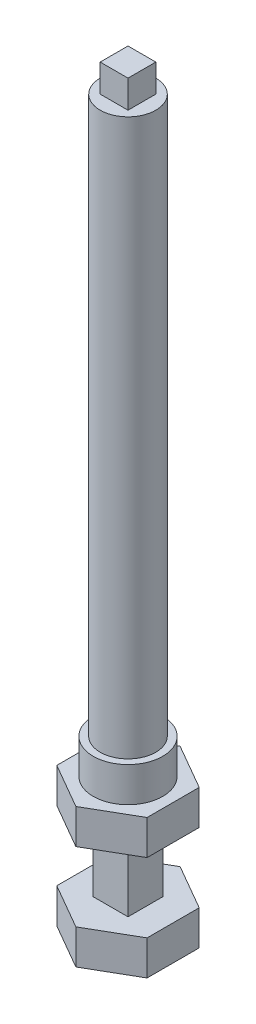
SolidWorks part; units mm, degrees
ref_plane "Front Plane" through (0, 0, 0) normal (0, 0, 1) x (1, 0, 0)
ref_plane "Top Plane" through (0, 0, 0) normal (0, 1, 0) x (1, 0, 0)
ref_plane "Right Plane" through (0, 0, 0) normal (1, 0, 0) x (0, 0, -1)
sketch "Sketch1" plane through (0, 0, 0) normal (0, 1, 0) x (1, 0, 0)
  line L1 (2.5, -2.5) -> (-2.5, -2.5)
  line L2 (2.5, -2.5) -> (2.5, 2.5)
  line L3 (2.5, 2.5) -> (-2.5, 2.5)
  line L4 (-2.5, -2.5) -> (-2.5, 2.5)
  line L5 (2.5, -2.5) -> (-2.5, 2.5) construction
  line L6 (2.5, 2.5) -> (-2.5, -2.5) construction
  point P0 (0, 0)
  dimension "D1" = 5
  dimension "D2" = 5
extrude "Boss-Extrude1" add sketch "Sketch1" along normal blind 10
sketch "Sketch2" plane through (0, 0, 0) normal (0, -1, 0) x (1, 0, 0)
  line L5 (0, 7.5) -> (-6.4952, 3.75)
  line L6 (-6.4952, 3.75) -> (-6.4952, -3.75)
  line L7 (-6.4952, -3.75) -> (0, -7.5)
  line L8 (0, -7.5) -> (6.4952, -3.75)
  line L9 (6.4952, -3.75) -> (6.4952, 3.75)
  line L10 (6.4952, 3.75) -> (0, 7.5)
  circle A0 centre (0, 0) radius 6.4952 construction
  point P0 (0, 0)
  dimension "D1" = 15
extrude "Boss-Extrude2" add sketch "Sketch2" along normal blind 5
sketch "Sketch3" plane through (0, 10, 0) normal (0, 1, 0) x (1, 0, 0)
  line L6 (0, -7.5) -> (6.4952, -3.75)
  line L7 (6.4952, -3.75) -> (6.4952, 3.75)
  line L8 (6.4952, 3.75) -> (0, 7.5)
  line L9 (0, 7.5) -> (-6.4952, 3.75)
  line L10 (-6.4952, 3.75) -> (-6.4952, -3.75)
  line L11 (-6.4952, -3.75) -> (0, -7.5)
  line L12 (0, -7.5) -> (6.4952, -3.75)
  line L13 (6.4952, -3.75) -> (6.4952, 3.75)
  line L14 (6.4952, 3.75) -> (0, 7.5)
  line L15 (0, 7.5) -> (-6.4952, 3.75)
  line L16 (-6.4952, 3.75) -> (-6.4952, -3.75)
  line L17 (-6.4952, -3.75) -> (0, -7.5)
  dimension "D1" = 0
extrude "Boss-Extrude3" add sketch "Sketch3" along normal blind 5
sketch "Sketch4" plane through (0, 15, 0) normal (0, 1, 0) x (1, 0, 0)
  circle A0 centre (0, 0) radius 5
  dimension "D1" = 10
extrude "Boss-Extrude4" add sketch "Sketch4" along normal blind 5
sketch "Sketch5" plane through (0, 20, 0) normal (0, 1, 0) x (1, 0, 0)
  circle A0 centre (0, 0) radius 4
  dimension "D1" = 8
extrude "Boss-Extrude5" add sketch "Sketch5" along normal offset from surface (80 mm away) 90 up to face at (0, 10, 0)
sketch "Sketch6" plane through (0, 100, 0) normal (0, 1, 0) x (1, 0, 0)
  line L1 (2, -2) -> (-2, -2)
  line L2 (2, -2) -> (2, 2)
  line L3 (2, 2) -> (-2, 2)
  line L4 (-2, -2) -> (-2, 2)
  line L5 (2, -2) -> (-2, 2) construction
  line L6 (2, 2) -> (-2, -2) construction
  point P0 (0, 0)
  dimension "D1" = 4
  dimension "D2" = 4
extrude "Boss-Extrude6" add sketch "Sketch6" along normal blind 4
